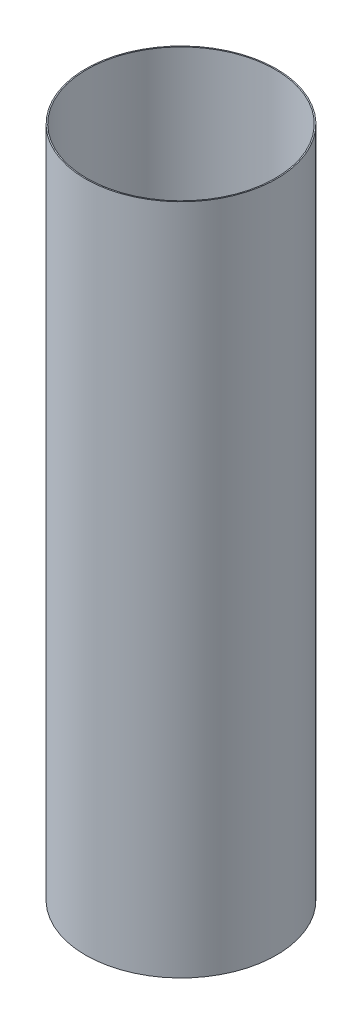
SolidWorks part; units mm, degrees
material "Hexcel AS4C (3000 Filaments)"
ref_plane "Front Plane" through (0, 0, 0) normal (0, 0, 1) x (1, 0, 0)
ref_plane "Top Plane" through (0, 0, 0) normal (0, 1, 0) x (1, 0, 0)
ref_plane "Right Plane" through (0, 0, 0) normal (1, 0, 0) x (0, 0, -1)
sketch "Sketch1" plane through (0, 0, 0) normal (0, 1, 0) x (1, 0, 0)
  circle A0 centre (0, 0) radius 83.439
  circle A1 centre (0, 0) radius 84.455
  dimension "D1" = 168.91
  dimension "D2" = 1.016
extrude "Boss-Extrude1" add sketch "Sketch1" along normal blind 595.0295
ref_plane "Plane1" through (0, 297.5148, 0) normal (0, 1, 0) x (1, 0, 0)
sketch "Sketch2" plane through (0, 0, 0) normal (0, 0, 1) x (1, 0, 0)
  line L0 (0, 3.81) -> (0, -68.0288) construction
  line L1 (3.175, 3.81) -> (3.175, -68.0288)
  line L2 (-3.175, 3.81) -> (-3.175, -68.0288)
  line L3 (-84.455, 0) -> (84.455, 0) construction
  arc A0 (3.175, 3.81) -> (-3.175, 3.81) centre (0, 3.81) ccw
  arc A1 (-3.175, -68.0288) -> (3.175, -68.0288) centre (0, -68.0288) ccw
  point P3 (0, -32.1094)
  dimension "D2" = 6.35
  dimension "D1" = 3.81
extrude "Cut-Extrude1" [suppressed] cut sketch "Sketch2" against normal through all
pattern_circular "CirPattern1" [suppressed] count 12 over 360
mirror "Mirror1" [suppressed] about plane through (0, 297.5148, 0) normal (0, 1, 0)
equation "\"nominalLength\"= 24in"
equation "\"interfaceOffset\"= 0.36217in - 0.1507 / 2in"
equation "\"sheetLength\"= \"nominalLength\" - 2 * \"interfaceOffset\""
equation "\"D1@Boss-Extrude1\"=\"sheetLength\""
